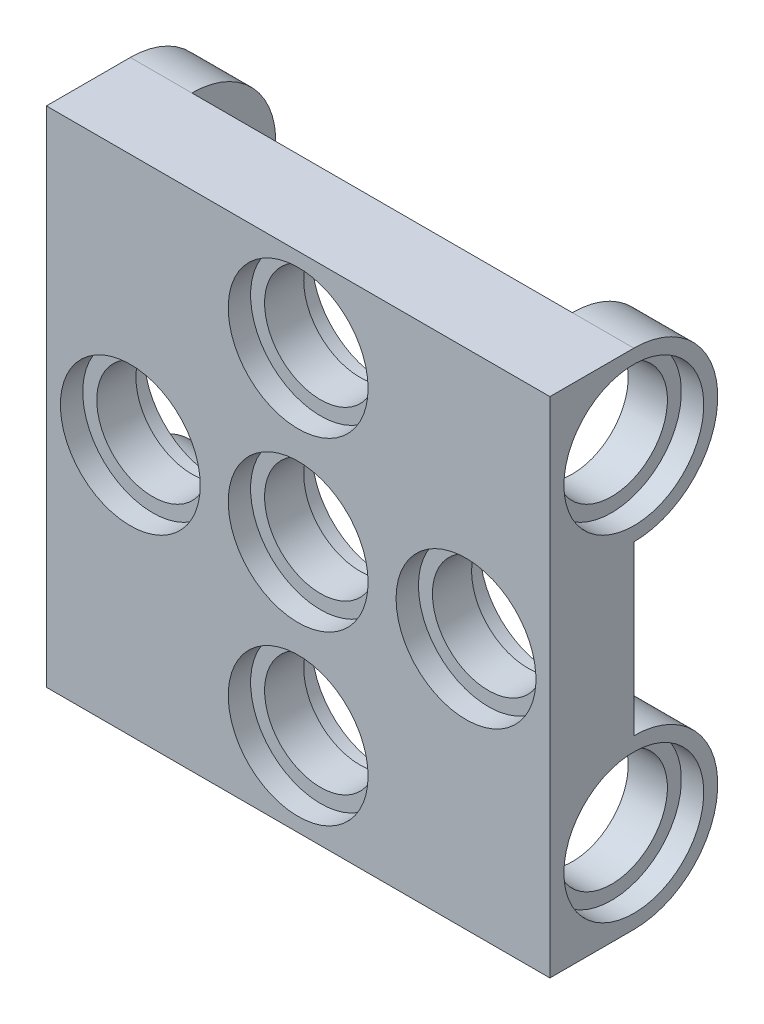
SolidWorks part; units mm, degrees
material "ABS"
ref_plane "Front Plane" through (0, 0, 0) normal (0, 0, 1) x (1, 0, 0)
ref_plane "Top Plane" through (0, 0, 0) normal (0, 1, 0) x (1, 0, 0)
ref_plane "Right Plane" through (0, 0, 0) normal (1, 0, 0) x (0, 0, -1)
sketch "Sketch1" plane through (0, 0, 0) normal (0, 0, 1) x (1, 0, 0)
  line L1 (0, 0) -> (-9, 0)
  line L2 (0, 0) -> (0, 9)
  line L3 (0, 9) -> (-9, 9)
  line L4 (-9, 0) -> (-9, 9)
  dimension "D1" = 9
extrude "Boss-Extrude1" add sketch "Sketch1" along normal blind 3
hole_wizard "Hole1" positions "Sketch3" profile "Sketch2" legacy end condition through all
sketch "Sketch3" plane through (0, 0, 3) normal (0, 0, 1) x (1, 0, 0)
  line L0 (-9, 0) -> (0, 0) construction
  line L1 (0, 0) -> (0, 9) construction
  point P0 (0, 0)
  point P3 (-6, 0)
  point P7 (0, 6)
  point P16 (-5.8556, 0)
  dimension "D1" = 6
  dimension "D2" = 6
sketch "Sketch2" plane through (0, 0, 3) normal (1, 0, 0) x (0, -1, 0)
  line L0 (0, 0) -> (0, 3)
  line L1 (0, 3) -> (2, 3)
  line L2 (2, 3) -> (2, 0.8)
  line L3 (2, 0.8) -> (2.5, 0.8)
  line L4 (2.5, 0.8) -> (2.5, 0)
  line L5 (2.5, 0) -> (0, 0)
  line L6 (0, 110) -> (0, -10) construction
  dimension "Diameter" = 4
  dimension "Depth" = 3
  dimension "C-Bore Diameter" = 5
  dimension "C-Bore Depth" = 0.8
sketch "Sketch4" plane through (-9, 0, 0) normal (-1, 0, 0) x (0, 0, 1)
  line L0 (0, 9) -> (0, 0) construction
  line L2 (0, 9) -> (0, 3)
  arc A0 (0, 9) -> (0, 3) centre (0, 6) ccw
  dimension "D1" = 6
extrude "Boss-Extrude3" add sketch "Sketch4" against normal blind 2.2
hole_wizard "Hole2" positions "Sketch6" profile "Sketch5" legacy end condition up to next
sketch "Sketch6" plane through (-9, 0, 0) normal (-1, 0, 0) x (0, 0, 1)
  arc A0 (0, 9) -> (0, 3) centre (0, 6) ccw construction
  point P0 (0, 6)
sketch "Sketch5" plane through (-9, 6, 0) normal (0, 1, 0) x (0, 0, 1)
  line L0 (0, 0) -> (0, 2.2)
  line L1 (0, 2.2) -> (2, 2.2)
  line L2 (2, 2.2) -> (2, 0.8)
  line L3 (2, 0.8) -> (2.5, 0.8)
  line L4 (2.5, 0.8) -> (2.5, 0)
  line L5 (2.5, 0) -> (0, 0)
  line L6 (0, 110) -> (0, -10) construction
  dimension "Diameter" = 4
  dimension "Depth" = 2.2
  dimension "C-Bore Diameter" = 5
  dimension "C-Bore Depth" = 0.8
sketch "Sketch7" plane through (0, 0, 0) normal (0, 0, -1) x (-1, 0, 0)
  circle A0 centre (0, 6) radius 2.5
  circle A1 centre (0, 0) radius 2.5
  circle A2 centre (6, 0) radius 2.5
  arc A3 (0, 3.5) -> (0, 8.5) centre (0, 6) ccw construction
  arc A4 (2.5, 0) -> (0, 2.5) centre (0, 0) ccw construction
  arc A5 (8.5, 0) -> (3.5, 0) centre (6, 0) ccw construction
extrude "Cut-Extrude1" cut sketch "Sketch7" against normal blind 0.8
sketch "Sketch8" plane through (-6.8, 0, 0) normal (1, 0, 0) x (0, 0, -1)
  line L0 (0, 4) -> (0, 8) construction
  circle A0 centre (0, 6) radius 2.5
  circle A1 centre (0, 6) radius 2.5 construction
extrude "Cut-Extrude2" cut sketch "Sketch8" along normal blind 0.8
mirror "Mirror1" about plane through (0, 0, 0) normal (1, 0, 0) of bodies 106
mirror "Mirror2" about plane through (0, 0, 0) normal (0, 1, 0) of bodies 107
equation "\"D2@Sketch3\"=\"D1@Sketch3\""
